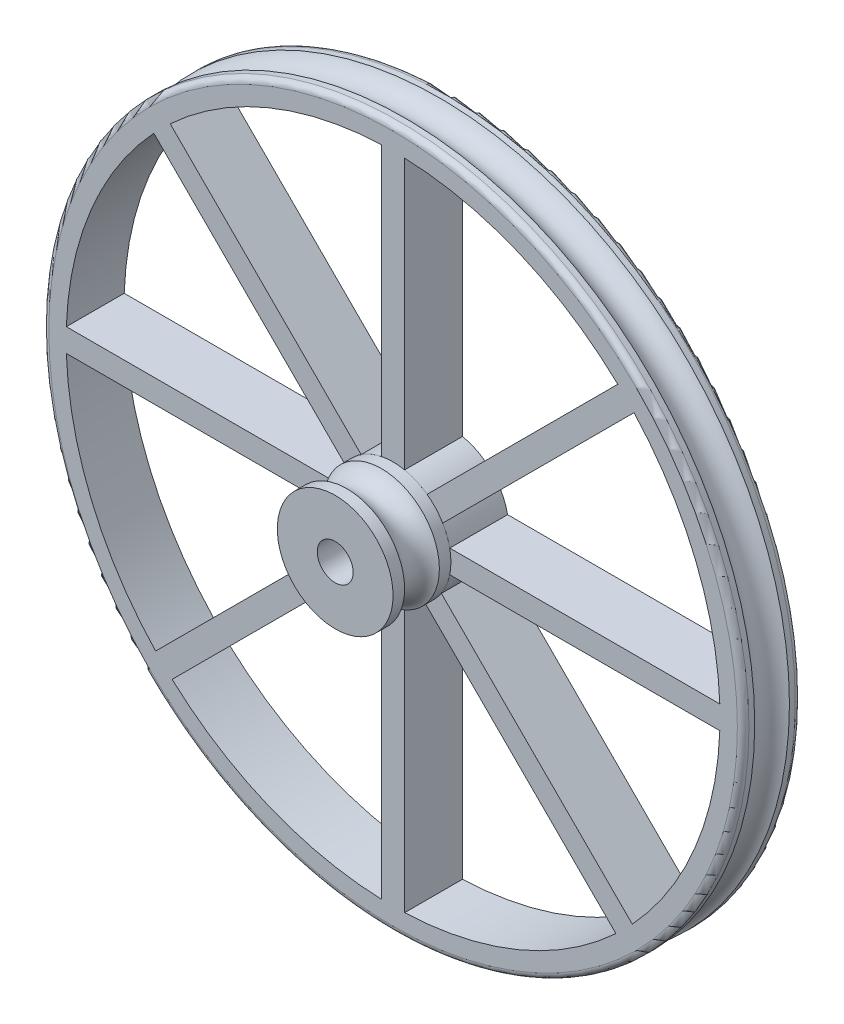
SolidWorks part; units mm, degrees
ref_plane "Front Plane" through (0, 0, 0) normal (0, 0, 1) x (1, 0, 0)
ref_plane "Top Plane" through (0, 0, 0) normal (0, 1, 0) x (1, 0, 0)
ref_plane "Right Plane" through (0, 0, 0) normal (1, 0, 0) x (0, 0, -1)
sketch "Sketch1" plane through (0, 0, 0) normal (0, 0, 1) x (1, 0, 0)
  circle A0 centre (0, 0) radius 29.75
  circle A1 centre (0, 0) radius 1.65
  dimension "D1" = 59.5
  dimension "D2" = 3.3
sketch "Sketch4" plane through (0, 0, 0) normal (1, 0, 0) x (0, 0, -1)
  line L0 (-5, 30.25) -> (-4, 30.25)
  line L1 (2.75, 0) -> (-2.75, 0) construction
  line L3 (0, 30.25) -> (-1, 30.25)
  line L7 (0, 30.25) -> (0, 0)
  line L8 (-5, 30.25) -> (-5, 0)
  line L10 (-5, 0) -> (0, 0)
  line L11 (0, 32.725) -> (0, -32.725) construction
  arc A0 (-4, 30.25) -> (-1, 30.25) centre (-2.5, 30.875) ccw
  point P15 (-2.5, 29.25)
  dimension "D2" = 30.25
  dimension "D1" = 1
  dimension "D3" = 1
revolve "Revolve1" add sketch "Sketch4" angle 360 about L10
sketch "Sketch6" plane through (0, 0, 0) normal (1, 0, 0) x (0, 0, -1)
  line L0 (-5, 0) -> (-5, 5)
  line L1 (-5, 5) -> (-6, 5)
  line L2 (-9, 5) -> (-10, 5)
  line L3 (-10, 5) -> (-10, 0)
  line L4 (-10, 0) -> (-5, 0)
  line L5 (-5, 30.25) -> (-5, -30.25) construction
  line L6 (2.75, 0) -> (-2.75, 0) construction
  arc A0 (-6, 5) -> (-9, 5) centre (-7.5, 5.625) cw
  point P8 (-7.5, 4)
  dimension "D1" = 1
  dimension "D2" = 1
  dimension "D3" = 5
  dimension "D4" = 5
revolve "Revolve2" add sketch "Sketch6" angle 360 about L4
sketch "Sketch7" plane through (0, 0, 0) normal (0, 0, 1) x (1, 0, 0)
  circle A0 centre (0, 0) radius 1.55
  dimension "D1" = 3.1
extrude "Cut-Extrude1" cut sketch "Sketch7" along normal blind 10
sketch "Sketch8" plane through (0, 0, 0) normal (0, 0, 1) x (1, 0, 0)
  line L10 (4.899, 1) -> (28.2323, 1)
  line L11 (1, 4.899) -> (1, 28.2323)
  line L12 (4.899, -1) -> (28.2323, -1)
  line L13 (1, -4.899) -> (1, -28.2323)
  line L14 (-1, -28.2323) -> (-1, -4.899)
  line L15 (-28.2323, -1) -> (-4.899, -1)
  line L16 (-28.2323, 1) -> (-4.899, 1)
  line L17 (-1, 4.899) -> (-1, 28.2323)
  line L18 (-22.4274, 22.4274) -> (22.4274, -22.4274) construction
  line L19 (0, 42.9618) -> (0, -48.1055) construction
  line L20 (-40.9984, 0) -> (49.712, 0) construction
  line L21 (5.5, 0) -> (-5.5, 0) construction
  line L22 (20.6704, -19.2561) -> (4.1712, -2.757)
  line L23 (-31.6023, -31.9162) -> (33.3304, 33.0165) construction
  line L24 (19.418, 20.5184) -> (2.9423, 4.0426)
  line L25 (20.8211, 19.093) -> (4.2924, 2.5643)
  line L26 (-20.5184, -19.418) -> (-4.0426, -2.9423)
  line L27 (-19.093, -20.8211) -> (-2.5643, -4.2924)
  line L28 (19.2561, -20.6704) -> (2.757, -4.1712)
  line L29 (-20.6704, 19.2561) -> (-4.1712, 2.757)
  line L30 (-19.2561, 20.6704) -> (-2.757, 4.1712)
  circle A1 centre (0, 0) radius 28.25 construction
  circle A12 centre (0, 0) radius 5 construction
  arc A13 (-19.2561, 20.6704) -> (-1, 28.2323) centre (0, 0) cw
  arc A14 (1, 28.2323) -> (19.418, 20.5184) centre (0, 0) cw
  arc A15 (20.8211, 19.093) -> (28.2323, 1) centre (0, 0) cw
  arc A16 (28.2323, -1) -> (20.6704, -19.2561) centre (0, 0) cw
  arc A17 (19.2561, -20.6704) -> (1, -28.2323) centre (0, 0) cw
  arc A18 (-1, -28.2323) -> (-19.093, -20.8211) centre (0, 0) cw
  arc A19 (-20.5184, -19.418) -> (-28.2323, -1) centre (0, 0) cw
  arc A20 (-28.2323, 1) -> (-20.6704, 19.2561) centre (0, 0) cw
  arc A21 (1, 4.899) -> (2.9423, 4.0426) centre (0, 0) ccw construction
  arc A22 (4.2924, 2.5643) -> (4.899, 1) centre (0, 0) cw
  arc A23 (4.899, -1) -> (4.1712, -2.757) centre (0, 0) cw
  arc A24 (2.757, -4.1712) -> (1, -4.899) centre (0, 0) cw
  arc A25 (-1, -4.899) -> (-2.5643, -4.2924) centre (0, 0) cw
  arc A26 (-4.0426, -2.9423) -> (-4.899, -1) centre (0, 0) cw
  arc A27 (-4.899, 1) -> (-4.1712, 2.757) centre (0, 0) cw
  arc A28 (-2.757, 4.1712) -> (-1, 4.899) centre (0, 0) cw
  arc A30 (1, 4.899) -> (2.9423, 4.0426) centre (0, 0) cw
  point P39 (0.864, 0.5502)
  point P48 (0, 0)
  dimension "D1" = 56.5
  dimension "D2" = 10
  dimension "D3" = 2
  dimension "D4" = 2
  dimension "D5" = 2
  dimension "D6" = 2
  dimension "D7" = 45
  dimension "D8" = 45
  dimension "D9" = 2
  dimension "D10" = 2
  dimension "D11" = 2
  dimension "D12" = 2
extrude "Cut-Extrude2" cut sketch "Sketch8" along normal blind 5
fillet "Fillet1" radius 0.5 2 edges at (30.25, 0, 0) (30.25, 0, 5)
